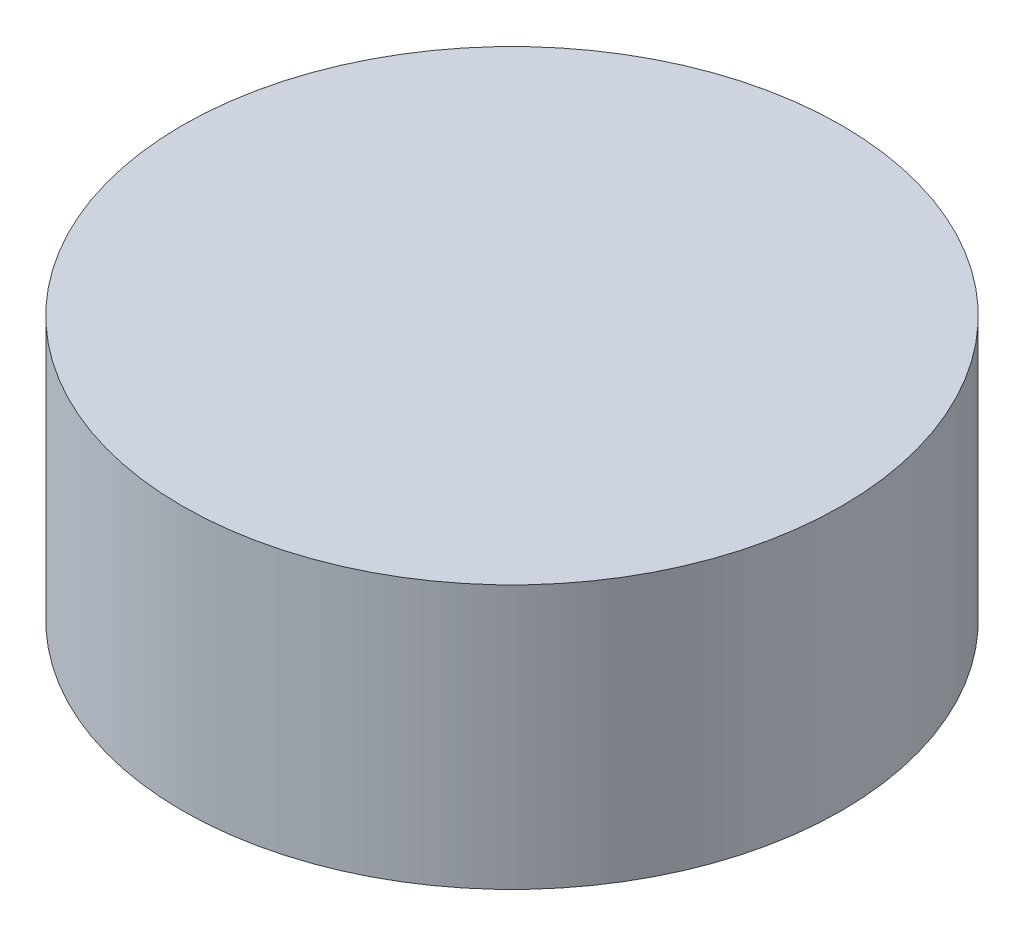
SolidWorks part; units mm, degrees
ref_plane "前基準面" through (0, 0, 0) normal (0, 0, 1) x (1, 0, 0)
ref_plane "上基準面" through (0, 0, 0) normal (0, 1, 0) x (1, 0, 0)
ref_plane "右基準面" through (0, 0, 0) normal (1, 0, 0) x (0, 0, -1)
sketch "草圖1" plane through (0, 0, 0) normal (0, 1, 0) x (1, 0, 0)
  circle A0 centre (0, 0) radius 5
  dimension "D1" = 10
extrude "填料-伸長1" add sketch "草圖1" along normal blind 4
